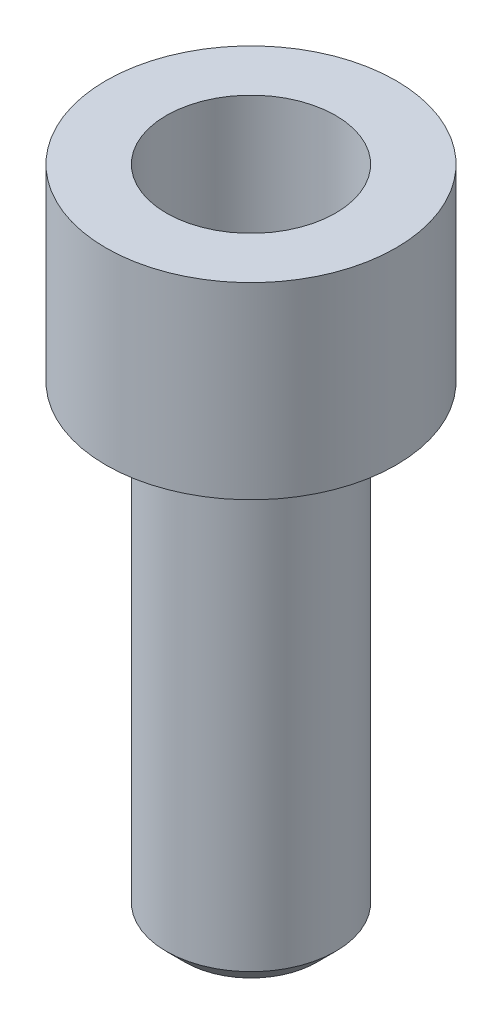
SolidWorks part; units mm, degrees
ref_plane "Alzado" through (0, 0, 0) normal (0, 0, 1) x (1, 0, 0)
ref_plane "Planta" through (0, 0, 0) normal (0, 1, 0) x (1, 0, 0)
ref_plane "Vista lateral" through (0, 0, 0) normal (1, 0, 0) x (0, 0, -1)
sketch "Croquis1" plane through (0, 0, 0) normal (0, 0, 1) x (1, 0, 0)
  line L0 (0, 15.2881) -> (0, -12.5902)
  line L1 (0, -12.5902) -> (3.5, -12.5902)
  line L2 (4.5, -11.5902) -> (4.5, 12.4098)
  line L3 (3.5, -12.5902) -> (4.5, -11.5902)
  line L4 (4.5, 12.4098) -> (7.7101, 12.4098)
  line L5 (7.7101, 12.4098) -> (7.7101, 22.4098)
  line L6 (7.7101, 22.4098) -> (4.5, 22.4098)
  line L7 (4.5, 22.4098) -> (4.5, 15.2881)
  line L8 (4.5, 15.2881) -> (0, 15.2881)
  line L11 (0, 27.3797) -> (0, -26.3539) construction
  point P4 (4.5, -12.5902)
  dimension "D2" = 25
  dimension "D3" = 10
revolve "Revolución2" add sketch "Croquis1" angle 360 about L11
